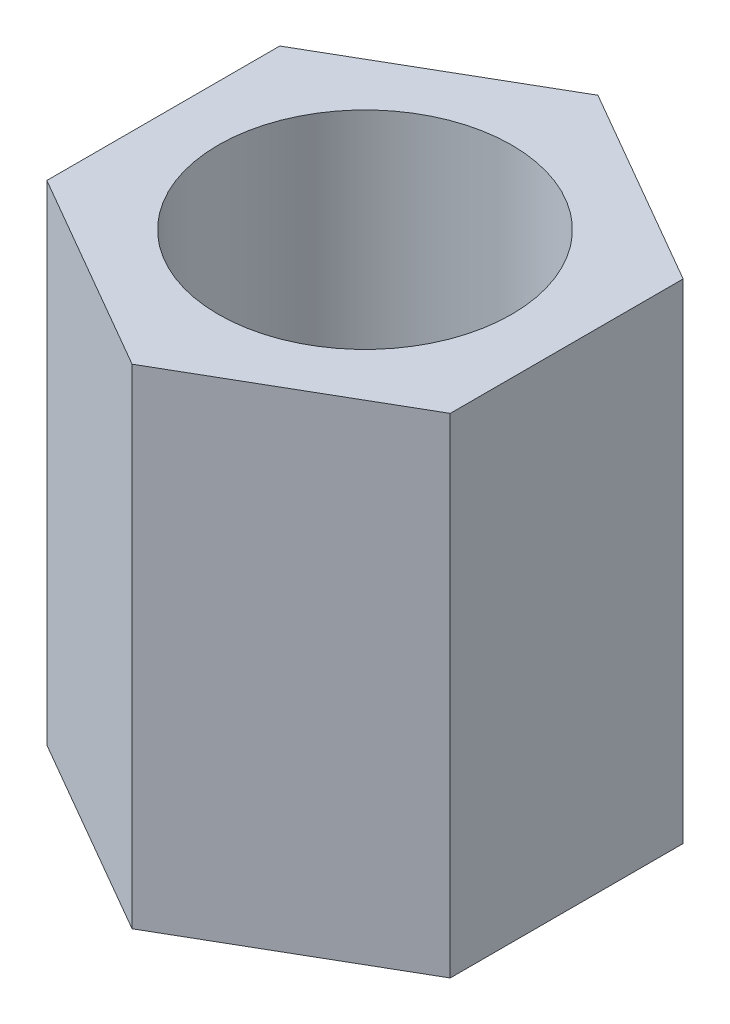
SolidWorks part; units mm, degrees
ref_plane "Front" through (0, 0, 0) normal (0, 0, 1) x (1, 0, 0)
ref_plane "Top" through (0, 0, 0) normal (0, 1, 0) x (1, 0, 0)
ref_plane "Right" through (0, 0, 0) normal (1, 0, 0) x (0, 0, -1)
sketch "草图1" plane through (0, 0, 0) normal (0, 1, 0) x (1, 0, 0)
  line L1 (0, 4.7631) -> (-4.125, 2.3816)
  line L2 (-4.125, 2.3816) -> (-4.125, -2.3816)
  line L3 (-4.125, -2.3816) -> (0, -4.7631)
  line L4 (0, -4.7631) -> (4.125, -2.3816)
  line L5 (4.125, -2.3816) -> (4.125, 2.3816)
  line L6 (4.125, 2.3816) -> (0, 4.7631)
  circle A0 centre (0, 0) radius 3
  circle A1 centre (0, 0) radius 4.125 construction
  dimension "D1" = 6
  dimension "D2" = 8.25
extrude "凸台-拉伸1" add sketch "草图1" along normal blind 10
